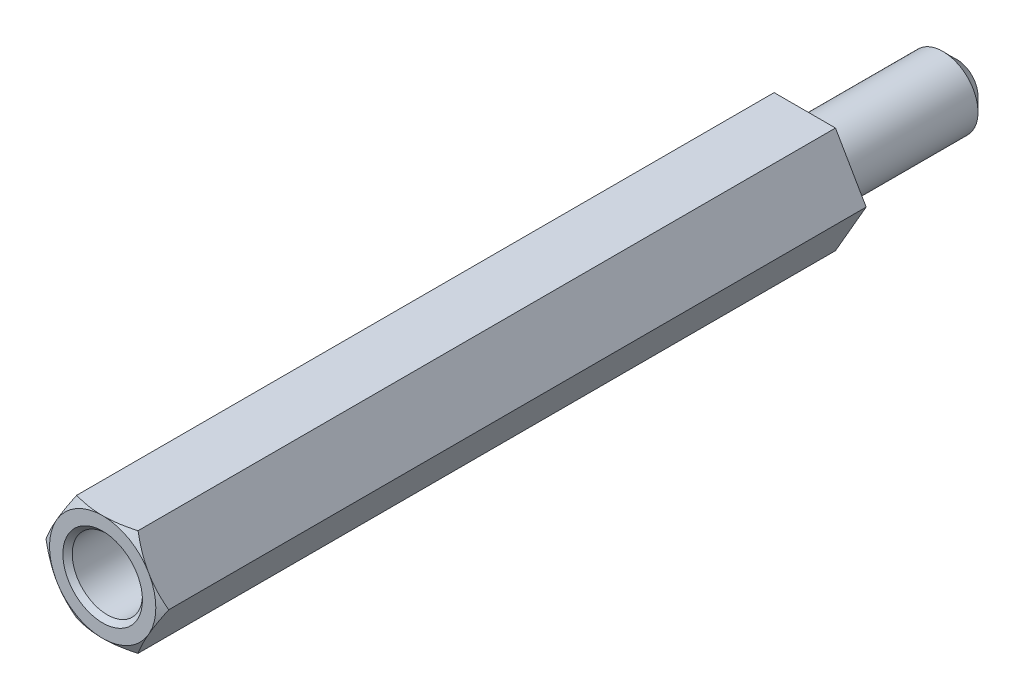
SolidWorks part; units mm, degrees
ref_plane "Front Plane" through (0, 0, 0) normal (0, 0, 1) x (1, 0, 0)
ref_plane "Top Plane" through (0, 0, 0) normal (0, 1, 0) x (1, 0, 0)
ref_plane "Right Plane" through (0, 0, 0) normal (1, 0, 0) x (0, 0, -1)
sketch "Sketch1" plane through (0, 0, 0) normal (0, 0, 1) x (1, 0, 0)
  line L0 (0, 0) -> (2.6212, 0) construction
  line L1 (2.6212, 0) -> (1.3106, 2.27)
  line L2 (1.3106, 2.27) -> (-1.3106, 2.27)
  line L3 (-1.3106, 2.27) -> (-2.6212, 0)
  line L4 (-2.6212, 0) -> (-1.3106, -2.27)
  line L5 (-1.3106, -2.27) -> (1.3106, -2.27)
  line L6 (1.3106, -2.27) -> (2.6212, 0)
  circle A0 centre (0, 0) radius 2.27 construction
  dimension "D1" = 4.54
extrude "Boss-Extrude1" add sketch "Sketch1" along normal blind 30
sketch "Sketch2" plane through (0, 0, 30) normal (0, 0, 1) x (1, 0, 0)
  circle A0 centre (0, 0) radius 1.5
extrude "Cut-Extrude1" cut sketch "Sketch2" against normal blind 12 and the other way through all
sketch "Sketch3" plane through (0, 0, 0) normal (0, 1, 0) x (1, 0, 0)
  line L0 (-2.6212, -30) -> (-2.2712, -30)
  line L1 (-2.2712, -30) -> (-2.6212, -29.8)
  line L2 (-2.6212, -30) -> (-2.6212, 0) construction
  line L3 (-2.6212, -29.8) -> (-2.6212, -30)
  dimension "D1" = 0.35
  dimension "D2" = 0.2
ref_axis "Axis1" through (0, 0, 18) along (0, 0, 1)
revolve "Cut-Revolve1" cut sketch "Sketch3" angle 360 about axis through (0, 0, 18) along (0, 0, 1)
ref_plane "Plane1" through (0, 0, 15) normal (0, 0, 1) x (1, 0, 0)
chamfer "Chamfer1" distance 0.2 angle 45 1 edges at (1.5, 0, 30)
sketch "Sketch4" plane through (0, 0, 0) normal (0, 0, -1) x (-1, 0, 0)
  circle A0 centre (0, 0) radius 1.5
extrude "Boss-Extrude2" add sketch "Sketch4" along normal blind 6.5
chamfer "Chamfer2" distance 0.6 angle 45 1 edges at (-1.5, 0, -6.5)
